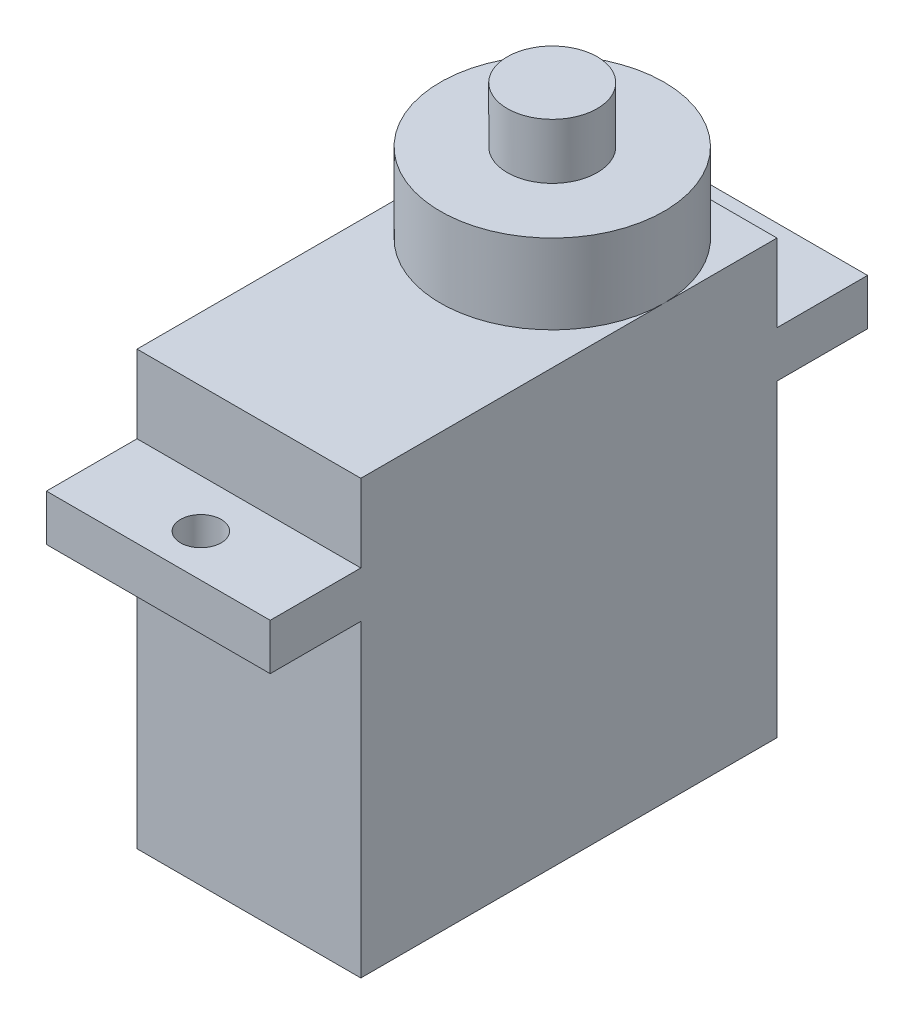
SolidWorks part; units mm, degrees
material "ABS"
ref_plane "Front Plane" through (0, 0, 0) normal (0, 0, 1) x (1, 0, 0)
ref_plane "Top Plane" through (0, 0, 0) normal (0, 1, 0) x (1, 0, 0)
ref_plane "Right Plane" through (0, 0, 0) normal (1, 0, 0) x (0, 0, -1)
sketch "Sketch1" plane through (0, 0, 0) normal (1, 0, 0) x (0, 0, -1)
  line L0 (0, 0) -> (22.5, 0)
  line L1 (22.5, 0) -> (22.5, 16.7)
  line L2 (22.5, 16.7) -> (27.4, 16.7)
  line L3 (27.4, 16.7) -> (27.4, 19.2)
  line L4 (27.4, 19.2) -> (22.5, 19.2)
  line L5 (22.5, 19.2) -> (22.5, 23.4)
  line L6 (22.5, 23.4) -> (0, 23.4)
  line L7 (0, 23.4) -> (0, 19.2)
  line L8 (0, 19.2) -> (-4.9, 19.2)
  line L9 (-4.9, 19.2) -> (-4.9, 16.7)
  line L10 (-4.9, 16.7) -> (0, 16.7)
  line L11 (0, 16.7) -> (0, 0)
  dimension "D1" = 22.5
  dimension "D2" = 16.7
  dimension "D3" = 23.4
  dimension "D4" = 19.2
  dimension "D5" = 32.3
extrude "Boss-Extrude1" add sketch "Sketch1" along normal blind 12.1
sketch "Sketch2" plane through (0, 19.2, 0) normal (0, 1, 0) x (1, 0, 0)
  line L0 (6.05, 25.1) -> (6.05, -2.6) construction
  line L1 (0, 11.25) -> (12.1, 11.25) construction
  line L2 (0, 22.5) -> (0, 0) construction
  line L3 (12.1, 22.5) -> (12.1, 0) construction
  circle A0 centre (6.05, -2.6) radius 1.1
  circle A1 centre (6.05, 25.1) radius 1.1
  point P11 (6.05, 11.25)
  dimension "D2" = 2.2
  dimension "D1" = 27.7
extrude "Cut-Extrude1" cut sketch "Sketch2" against normal through all
ref_plane "Plane1" through (0, 27.7, 0) normal (0, -1, 0) x (-1, 0, 0)
ref_plane "Plane2" through (0, 30.7, 0) normal (0, -1, 0) x (-1, 0, 0)
sketch "Sketch3" plane through (0, 23.4, 0) normal (0, 1, 0) x (1, 0, 0)
  line L0 (6.05, 22.5) -> (6.05, 0) construction
  line L1 (12.1, 22.5) -> (0, 22.5) construction
  line L2 (12.1, 0) -> (0, 0) construction
  line L3 (12.1, 22.5) -> (12.1, 0) construction
  circle A0 centre (6.05, 16.4) radius 6.05
  circle A1 centre (6.05, 25.1) radius 1.1 construction
  dimension "D1" = 8.7
extrude "Boss-Extrude3" add sketch "Sketch3" along normal up to surface (4.3 mm away) up to plane "Plane1"
sketch "Sketch4" plane through (0, 27.7, 0) normal (0, 1, 0) x (1, 0, 0)
  circle A0 centre (6.05, 16.4) radius 2.43
  arc A1 (0, 16.4) -> (12.1, 16.4) centre (6.05, 16.4) ccw construction
  dimension "D1" = 4.86
extrude "Boss-Extrude4" add sketch "Sketch4" along normal up to surface (3 mm away) up to plane "Plane2"
